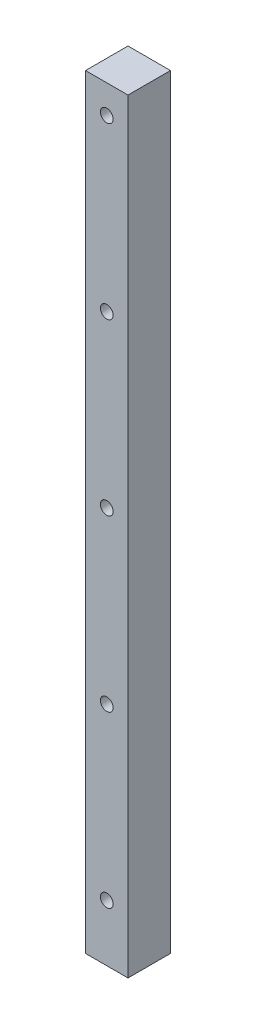
SolidWorks part; units mm, degrees
ref_plane "前视基准面" through (0, 0, 0) normal (0, 0, 1) x (1, 0, 0)
ref_plane "上视基准面" through (0, 0, 0) normal (0, 1, 0) x (1, 0, 0)
ref_plane "右视基准面" through (0, 0, 0) normal (1, 0, 0) x (0, 0, -1)
other "Configuration Table"
sketch "草图1" plane through (0, 0, 0) normal (0, 1, 0) x (1, 0, 0)
  line L1 (7.5, -7.5) -> (-7.5, -7.5)
  line L2 (7.5, -7.5) -> (7.5, 7.5)
  line L3 (7.5, 7.5) -> (-7.5, 7.5)
  line L4 (-7.5, -7.5) -> (-7.5, 7.5)
  line L5 (7.5, -7.5) -> (-7.5, 7.5) construction
  line L6 (7.5, 7.5) -> (-7.5, -7.5) construction
  point P0 (0, 0)
  dimension "D1" = 15
  dimension "D2" = 15
extrude "凸台-拉伸1" add sketch "草图1" along normal blind 270
sketch "草图2" plane through (0, 0, -7.5) normal (0, 0, -1) x (-1, 0, 0)
  circle A0 centre (0, 20) radius 2.25
  circle A1 centre (0, 80) radius 2.25
  circle A2 centre (0, 140) radius 2.25
  circle A3 centre (0, 200) radius 2.25
  circle A4 centre (0, 260) radius 2.25
  dimension "D1" = 4.5
  dimension "D2" = 20
  dimension "D3" = 2
  dimension "D4" = 4
extrude "切除-拉伸1" cut sketch "草图2" against normal blind 119
